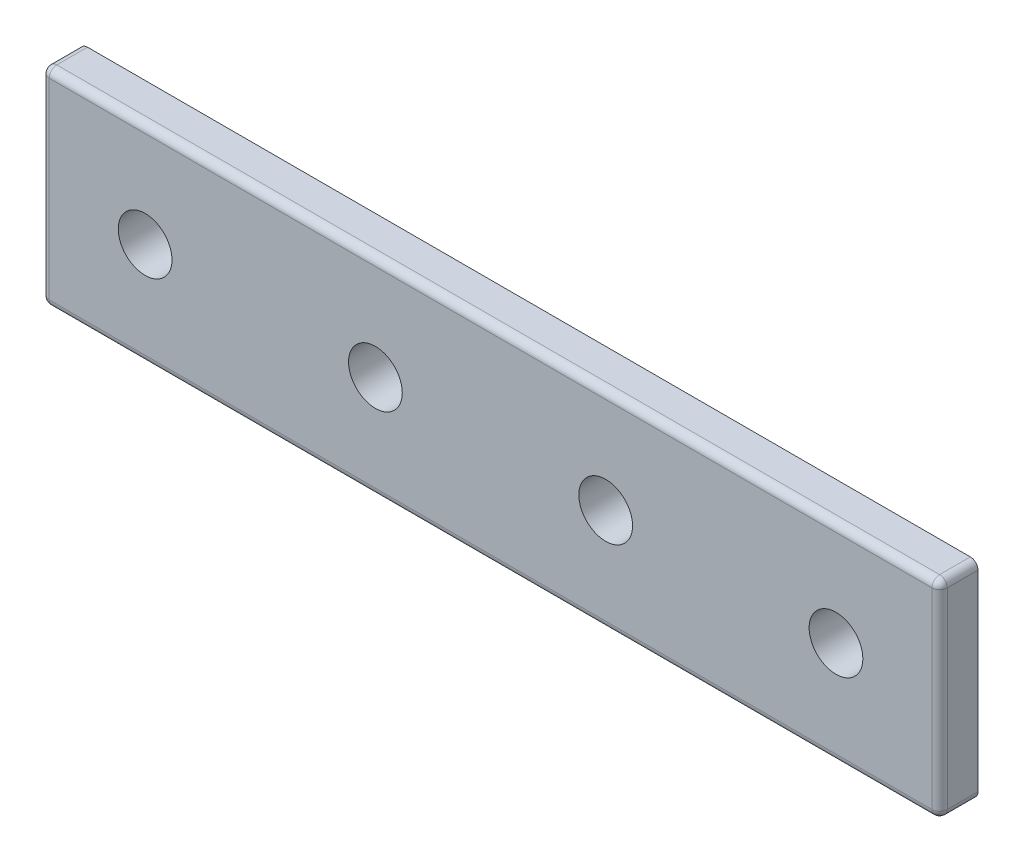
SolidWorks part; units mm, degrees
ref_plane "Front Plane" through (0, 0, 0) normal (0, 0, 1) x (1, 0, 0)
ref_plane "Top Plane" through (0, 0, 0) normal (0, 1, 0) x (1, 0, 0)
ref_plane "Right Plane" through (0, 0, 0) normal (1, 0, 0) x (0, 0, -1)
sketch "Sketch1" plane through (0, 0, 0) normal (0, 0, 1) x (1, 0, 0)
  line L0 (0, 0) -> (0, 27)
  line L1 (13.5, 13.5) -> (43.5, 13.5) construction
  line L2 (43.5, 13.5) -> (73.5, 13.5) construction
  line L3 (73.5, 13.5) -> (103.5, 13.5) construction
  line L4 (117, 27) -> (0, 27)
  line L5 (117, 0) -> (0, 0)
  line L7 (117, 27) -> (117, 0)
  circle A0 centre (13.5, 13.5) radius 3.5
  circle A1 centre (43.5, 13.5) radius 3.5
  circle A2 centre (73.5, 13.5) radius 3.5
  circle A3 centre (103.5, 13.5) radius 3.5
  dimension "D1" = 30
  dimension "E" = 7
  dimension "D2" = 13.5
  dimension "C" = 27
  dimension "D3" = 13.5
  dimension "B" = 117
extrude "Boss-Extrude1" add sketch "Sketch1" along normal mid plane 5
fillet "Fillet1" radius 1 8 edges at (0, 0, 0) (0, 13.5, 2.5) (58.5, 0, 2.5) (117, 13.5, 2.5) (117, 0, 0) (117, 27, 0) (58.5, 27, 2.5) (0, 27, 0)
